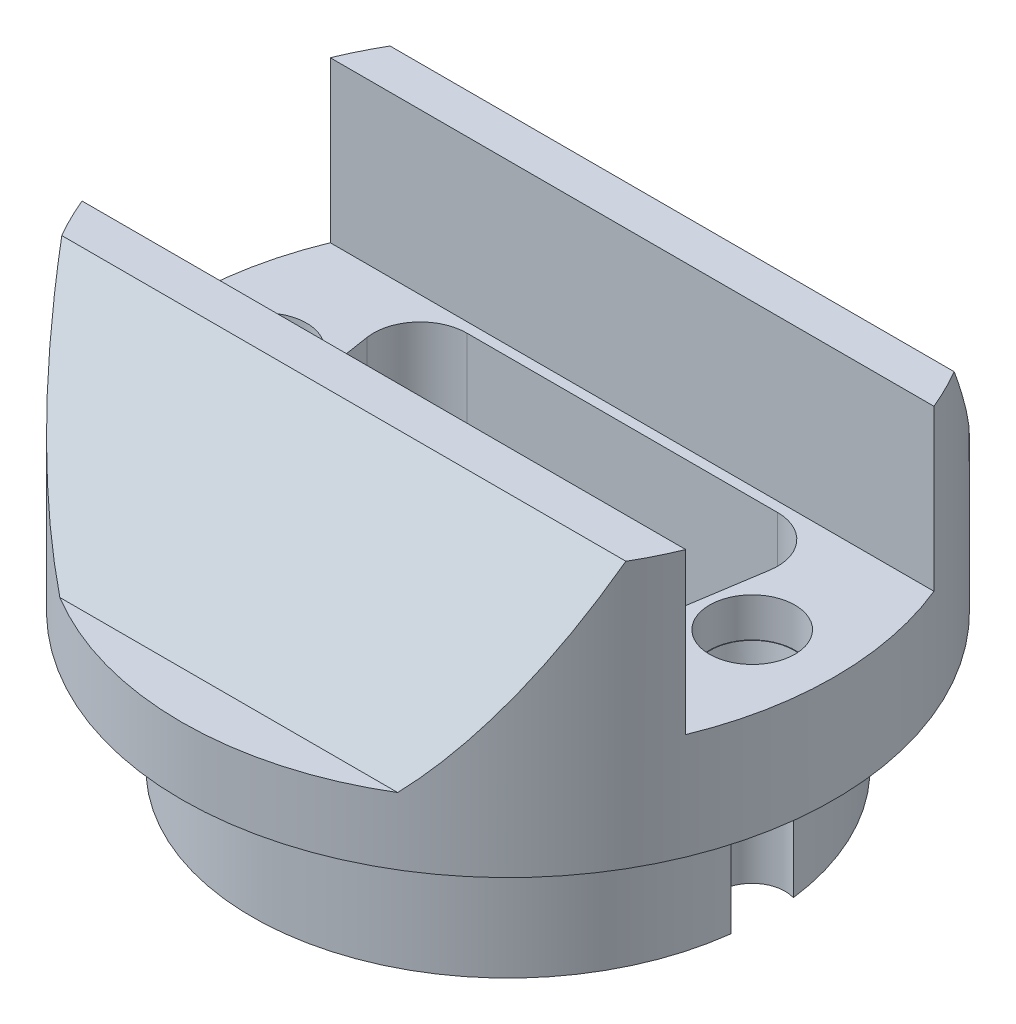
SolidWorks part; units mm, degrees
material "6061-T6 (SS)"
ref_plane "Front Plane" through (0, 0, 0) normal (0, 0, 1) x (1, 0, 0)
ref_plane "Top Plane" through (0, 0, 0) normal (0, 1, 0) x (1, 0, 0)
ref_plane "Right Plane" through (0, 0, 0) normal (1, 0, 0) x (0, 0, -1)
sketch "Sketch1" plane through (0, 0, 0) normal (0, 1, 0) x (1, 0, 0)
  circle A0 centre (0, 0) radius 13.1
  dimension "D1" = 26.2
extrude "Boss-Extrude1" add sketch "Sketch1" along normal blind 7
ref_plane "Plane4" through (0, 10.429, 0) normal (0, 1, 0) x (1, 0, 0)
sketch "Sketch2" plane through (0, 7, 0) normal (0, 1, 0) x (1, 0, 0)
  circle A0 centre (0, 0) radius 16.7
  dimension "D1" = 33.4
extrude "Boss-Extrude2" add sketch "Sketch2" along normal up to surface (3.429 mm away) up to plane "Plane4"
sketch "Sketch3" plane through (0, 10.429, 0) normal (0, 1, 0) x (1, 0, 0)
  line L0 (-7.9502, 5.842) -> (7.9502, 5.842)
  line L1 (10.3092, 3.0858) -> (9.2297, -3.823)
  line L2 (6.8707, -5.842) -> (-6.8707, -5.842)
  line L3 (-9.2297, -3.823) -> (-10.3092, 3.0858)
  line L4 (0, 0) -> (0, 5.842) construction
  line L5 (0, 0) -> (0, -5.842) construction
  circle A0 centre (-12.4968, 0) radius 2.1844
  circle A1 centre (12.4968, 0) radius 2.1844
  arc A2 (-7.9502, 5.842) -> (-10.3092, 3.0858) centre (-7.9502, 3.4544) ccw
  arc A3 (7.9502, 5.842) -> (10.3092, 3.0858) centre (7.9502, 3.4544) cw
  arc A4 (9.2297, -3.823) -> (6.8707, -5.842) centre (6.8707, -3.4544) cw
  arc A5 (-9.2297, -3.823) -> (-6.8707, -5.842) centre (-6.8707, -3.4544) ccw
  dimension "D1" = 2.3876
  dimension "D7" = 4.3688
  dimension "D2" = 15.9004
  dimension "D3" = 13.7414
  dimension "D4" = 24.9936
  dimension "D5" = 12.4968
  dimension "D6" = 5.842
extrude "Cut-Extrude1" cut sketch "Sketch3" against normal through all contours L3 A5 L2 A4 L1 A3 L0 A2
sketch "Sketch4" plane through (0, 10.429, 0) normal (0, 1, 0) x (1, 0, 0)
  line L1 (-19.05, -6.35) -> (19.05, -6.35)
  line L2 (-19.05, -6.35) -> (-19.05, 6.35)
  line L3 (-19.05, 6.35) -> (19.05, 6.35)
  line L4 (19.05, -6.35) -> (19.05, 6.35)
  line L5 (-19.05, -6.35) -> (19.05, 6.35) construction
  line L6 (-19.05, 6.35) -> (19.05, -6.35) construction
  point P0 (0, 0)
  dimension "D1" = 12.7
  dimension "D2" = 38.1
sketch "Sketch5" plane through (0, 10.429, 0) normal (0, 1, 0) x (1, 0, 0)
  circle A0 centre (12.4968, 0) radius 2.159
  circle A1 centre (-12.4968, 0) radius 2.159
  dimension "D1" = 4.318
extrude "Cut-Extrude2" cut sketch "Sketch5" against normal up to surface (3.429 mm away) draft 8
sketch "Sketch6" plane through (0, 7, 0) normal (0, 1, 0) x (1, 0, 0)
  arc A2 (13.002, -1.5992) -> (13.002, 1.5992) centre (0, 0) ccw
  arc A3 (13.002, 1.5992) -> (13.002, -1.5992) centre (12.4968, 0) ccw
  arc A4 (13.002, -1.5992) -> (13.002, 1.5992) centre (0, 0) ccw
  arc A5 (13.002, 1.5992) -> (13.002, -1.5992) centre (12.4968, 0) ccw
  arc A6 (-13.002, 1.5992) -> (-13.002, -1.5992) centre (0, 0) ccw
  arc A7 (-13.002, -1.5992) -> (-13.002, 1.5992) centre (-12.4968, 0) ccw
  arc A8 (-13.002, 1.5992) -> (-13.002, -1.5992) centre (0, 0) ccw
  arc A9 (-13.002, -1.5992) -> (-13.002, 1.5992) centre (-12.4968, 0) ccw
  dimension "D1" = 0
  dimension "D2" = 0
extrude "Cut-Extrude3" cut sketch "Sketch6" against normal through all
ref_plane "Plane5" through (0, 18.629, 0) normal (0, 1, 0) x (1, 0, 0)
ref_plane "Plane6" through (0, 20.629, 0) normal (0, 1, 0) x (1, 0, 0)
ref_plane "Plane7" through (16.7, 0, 0) normal (1, 0, 0) x (0, 0, -1)
sketch "Sketch7" plane through (0, 10.429, 0) normal (0, 1, 0) x (1, 0, 0)
  circle A1 centre (0, 0) radius 16.7
  circle A2 centre (0, 0) radius 16.7
  dimension "D1" = 0
extrude "Boss-Extrude3" add sketch "Sketch7" along normal up to surface (10.2 mm away) up to plane "Plane6"
sketch "Sketch9" plane through (16.7, 0, 0) normal (1, 0, 0) x (0, 0, -1)
  line L0 (0, 10.429) -> (0, 20.629) construction
  line L2 (55, 10.429) -> (-55, 10.429) construction
  line L3 (55, 20.629) -> (-55, 20.629) construction
  line L4 (6.35, 20.629) -> (-6.35, 20.629)
  line L5 (-6.35, 10.429) -> (-6.35, 20.629)
  line L6 (-6.35, 10.429) -> (6.35, 10.429)
  line L7 (-6.35, 20.629) -> (-6.35, 10.429) construction
  line L8 (6.35, 20.629) -> (6.35, 10.429) construction
  line L9 (6.35, 10.429) -> (6.35, 20.629)
  line L10 (-17.4694, 10.429) -> (-14.289, 10.429)
  line L11 (-14.289, 10.429) -> (-8.4, 20.629)
  line L12 (-8.4, 20.629) -> (-17.4694, 20.629)
  line L13 (-17.4694, 20.629) -> (-17.4694, 10.429)
  line L14 (17.4694, 20.629) -> (17.4694, 10.429)
  line L15 (8.4, 20.629) -> (17.4694, 20.629)
  line L16 (14.289, 10.429) -> (8.4, 20.629)
  line L17 (17.4694, 10.429) -> (14.289, 10.429)
  dimension "D1" = 60
  dimension "D2" = 2.05
extrude "Cut-Extrude4" cut sketch "Sketch9" against normal through all
sketch "Sketch10" plane through (0, 10.429, 0) normal (0, 1, 0) x (1, 0, 0)
  line L0 (6.8707, -5.842) -> (-6.8707, -5.842) construction
  line L1 (10.3092, 3.0858) -> (9.2297, -3.823) construction
  line L2 (15.4456, 6.35) -> (-15.4456, 6.35)
  line L3 (-15.4456, -6.35) -> (15.4456, -6.35)
  line L4 (15.4456, 6.35) -> (-15.4456, 6.35)
  line L5 (-15.4456, -6.35) -> (15.4456, -6.35)
  line L6 (-7.9502, 5.842) -> (7.9502, 5.842) construction
  line L7 (-9.2297, -3.823) -> (-10.3092, 3.0858) construction
  line L8 (6.8707, -5.842) -> (-6.8707, -5.842)
  line L9 (10.3092, 3.0858) -> (9.2297, -3.823)
  line L10 (-7.9502, 5.842) -> (7.9502, 5.842)
  line L11 (-9.2297, -3.823) -> (-10.3092, 3.0858)
  circle A0 centre (12.4968, 0) radius 2.1844 construction
  circle A1 centre (-12.4968, 0) radius 2.1844 construction
  arc A2 (-15.4456, 6.35) -> (-15.4456, -6.35) centre (0, 0) ccw
  arc A3 (15.4456, -6.35) -> (15.4456, 6.35) centre (0, 0) ccw
  arc A4 (-15.4456, 6.35) -> (-15.4456, -6.35) centre (0, 0) ccw
  arc A5 (15.4456, -6.35) -> (15.4456, 6.35) centre (0, 0) ccw
  arc A6 (6.8707, -5.842) -> (9.2297, -3.823) centre (6.8707, -3.4544) ccw construction
  arc A7 (10.3092, 3.0858) -> (7.9502, 5.842) centre (7.9502, 3.4544) ccw construction
  arc A8 (-7.9502, 5.842) -> (-10.3092, 3.0858) centre (-7.9502, 3.4544) ccw construction
  arc A9 (-9.2297, -3.823) -> (-6.8707, -5.842) centre (-6.8707, -3.4544) ccw construction
  circle A10 centre (12.4968, 0) radius 2.1844
  circle A11 centre (-12.4968, 0) radius 2.1844
  arc A12 (6.8707, -5.842) -> (9.2297, -3.823) centre (6.8707, -3.4544) ccw
  arc A13 (10.3092, 3.0858) -> (7.9502, 5.842) centre (7.9502, 3.4544) ccw
  arc A14 (-7.9502, 5.842) -> (-10.3092, 3.0858) centre (-7.9502, 3.4544) ccw
  arc A15 (-9.2297, -3.823) -> (-6.8707, -5.842) centre (-6.8707, -3.4544) ccw
  dimension "D1" = 0
extrude "Boss-Extrude4" add sketch "Sketch10" along normal blind 2
ref_plane "Plane1" through (-16.7, 0, 0) normal (-1, 0, 0) x (0, 0, 1)
